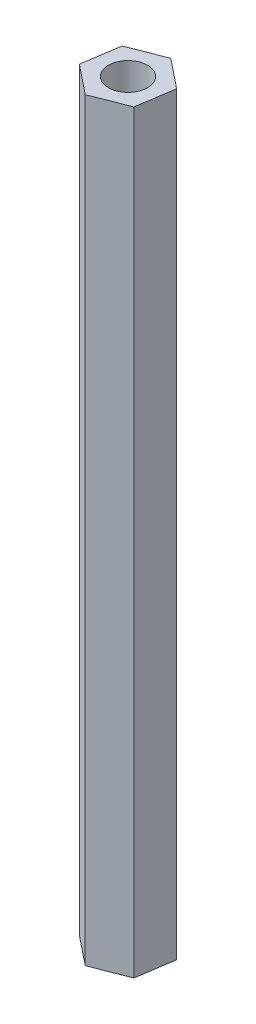
SolidWorks part; units mm, degrees
ref_plane "Front Plane" through (0, 0, 0) normal (0, 0, 1) x (1, 0, 0)
ref_plane "Top Plane" through (0, 0, 0) normal (0, 1, 0) x (1, 0, 0)
ref_plane "Right Plane" through (0, 0, 0) normal (1, 0, 0) x (0, 0, -1)
sketch "Sketch1" plane through (0, 0, 0) normal (0, 1, 0) x (1, 0, 0)
  line L1 (2.2542, -1.8033) -> (2.6888, 1.0505)
  line L2 (2.6888, 1.0505) -> (0.4347, 2.8538)
  line L3 (0.4347, 2.8538) -> (-2.2542, 1.8033)
  line L4 (-2.2542, 1.8033) -> (-2.6888, -1.0505)
  line L5 (-2.6888, -1.0505) -> (-0.4347, -2.8538)
  line L6 (-0.4347, -2.8538) -> (2.2542, -1.8033)
  circle A0 centre (0, 0) radius 1.5
  circle A1 centre (0, 0) radius 2.5 construction
  dimension "D1" = 3
  dimension "D2" = 5
extrude "Boss-Extrude1" add sketch "Sketch1" along normal blind 58
